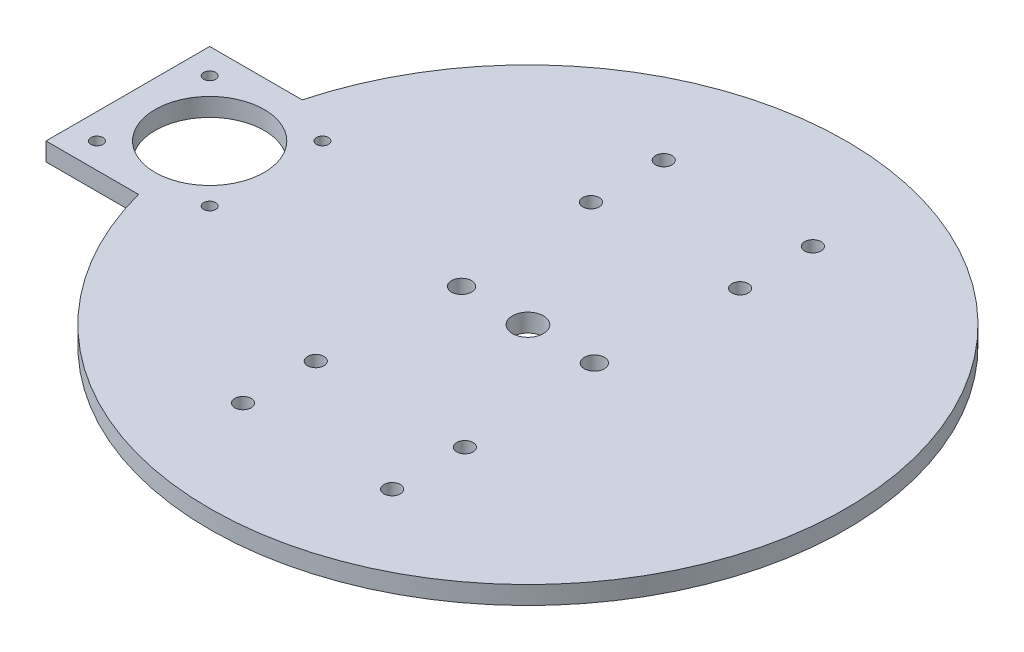
SolidWorks part; units mm, degrees
ref_plane "Front Plane" through (0, 0, 0) normal (0, 0, 1) x (1, 0, 0)
ref_plane "Top Plane" through (0, 0, 0) normal (0, 1, 0) x (1, 0, 0)
ref_plane "Right Plane" through (0, 0, 0) normal (1, 0, 0) x (0, 0, -1)
sketch "Sketch2" plane through (0, 0, 0) normal (0, 1, 0) x (1, 0, 0)
  line L0 (0, 87.5) -> (0, -87.5) construction
  line L1 (-110, 22.5) -> (-65, 22.5)
  line L2 (-110, 22.5) -> (-110, -22.5)
  line L3 (-110, -22.5) -> (-65, -22.5)
  line L4 (-65, 22.5) -> (-65, -22.5) construction
  line L5 (-110, 22.5) -> (-65, -22.5) construction
  line L6 (-110, -22.5) -> (-65, 22.5) construction
  line L7 (-66.5, -21) -> (-108.5, -21) construction
  line L8 (-66.5, -21) -> (-66.5, 21) construction
  line L9 (-66.5, 21) -> (-108.5, 21) construction
  line L10 (-108.5, -21) -> (-108.5, 21) construction
  line L11 (-66.5, -21) -> (-108.5, 21) construction
  line L12 (-66.5, 21) -> (-108.5, -21) construction
  line L13 (-87.5, 0) -> (87.5, 0) construction
  line L18 (0, 0) -> (-2.0021, 3.7489)
  line L19 (-27.269, 51.0612) -> (-27.7935, 52.0434)
  line L20 (0, 0) -> (2.0021, 3.7489)
  line L21 (27.269, 51.0612) -> (27.7935, 52.0434)
  line L22 (0, 0) -> (2.0021, -3.7489)
  line L23 (27.269, -51.0612) -> (27.7935, -52.0434)
  line L24 (-27.269, -51.0612) -> (-27.7935, -52.0434)
  line L25 (0, 0) -> (-2.0021, -3.7489)
  line L26 (-25.4381, 47.633) -> (-27.269, 51.0612)
  line L27 (25.4381, 47.633) -> (27.269, 51.0612)
  line L32 (-25.4381, -47.633) -> (-27.269, -51.0612)
  line L33 (25.4381, -47.633) -> (27.269, -51.0612)
  circle A0 centre (0, 0) radius 78.75 construction
  circle A2 centre (-87.5, 0) radius 8.75 construction
  circle A3 centre (0, 0) radius 87.5
  circle A4 centre (-87.5, 0) radius 15
  circle A5 centre (-103, 15.5) radius 1.65
  circle A6 centre (-72, 15.5) radius 1.65
  circle A7 centre (-72, -15.5) radius 1.65
  circle A8 centre (-103, -15.5) radius 1.65
  arc A9 (-27.7935, 52.0434) -> (-27.7935, -52.0434) centre (0, 0) ccw
  arc A10 (-25.4381, 47.633) -> (-25.4381, -47.633) centre (0, 0) ccw
  circle A11 centre (0, 0) radius 4.25
  circle A12 centre (18.25, 0) radius 2.75
  circle A13 centre (-18.25, 0) radius 2.75
  circle A14 centre (-20.5, 57.8302) radius 2.25
  circle A15 centre (20.5, 57.8302) radius 2.25
  circle A16 centre (20.5, 37.8302) radius 2.25
  circle A17 centre (-20.5, 37.8302) radius 2.25
  circle A18 centre (-20.5, -37.8302) radius 2.25
  circle A19 centre (20.5, -37.8302) radius 2.25
  circle A20 centre (20.5, -57.8302) radius 2.25
  circle A21 centre (-20.5, -57.8302) radius 2.25
  circle A22 centre (-20.5, 57.8302) radius 4
  circle A23 centre (20.5, 57.8302) radius 4
  circle A24 centre (-20.5, -57.8302) radius 4
  circle A25 centre (20.5, -57.8302) radius 4
  arc A29 (25.4381, -47.633) -> (25.4381, 47.633) centre (0, 0) ccw
  arc A31 (27.7935, -52.0434) -> (27.7935, 52.0434) centre (0, 0) ccw
  point P32 (0, 47.8302)
  point P55 (0, -47.8302)
  dimension "D1" = 175
  dimension "D2" = 157.5
  dimension "D3" = 45
  dimension "D5" = 17.5
  dimension "D6" = 5.5
  dimension "D10" = 18.25
  dimension "D11" = 36.5
  dimension "D14" = 2
  dimension "D4" = 45
  dimension "D7" = 42
  dimension "D8" = 2
  dimension "D9" = 2
  dimension "D15" = 2
extrude "Boss-Extrude3" add sketch "Sketch2" along normal blind 5
